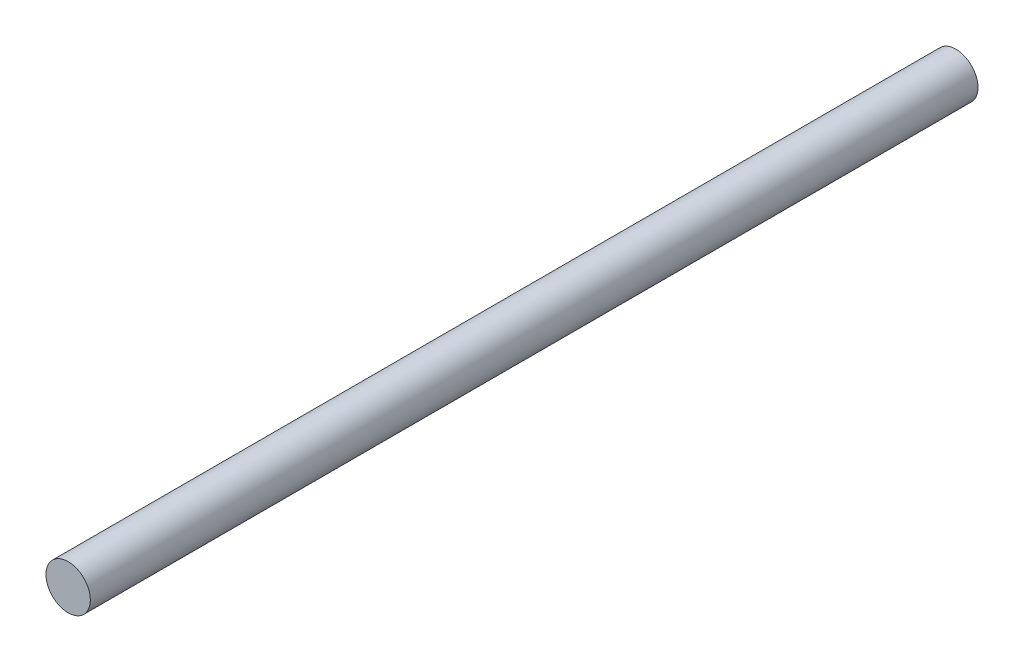
SolidWorks part; units mm, degrees
ref_plane "前视基准面" through (0, 0, 0) normal (0, 0, 1) x (1, 0, 0)
ref_plane "上视基准面" through (0, 0, 0) normal (0, 1, 0) x (1, 0, 0)
ref_plane "右视基准面" through (0, 0, 0) normal (1, 0, 0) x (0, 0, -1)
sketch "草图1" plane through (0, 0, 0) normal (0, 0, 1) x (1, 0, 0)
  circle A0 centre (0, 0) radius 2
  dimension "D1" = 4
extrude "凸台-拉伸1" add sketch "草图1" along normal blind 80
